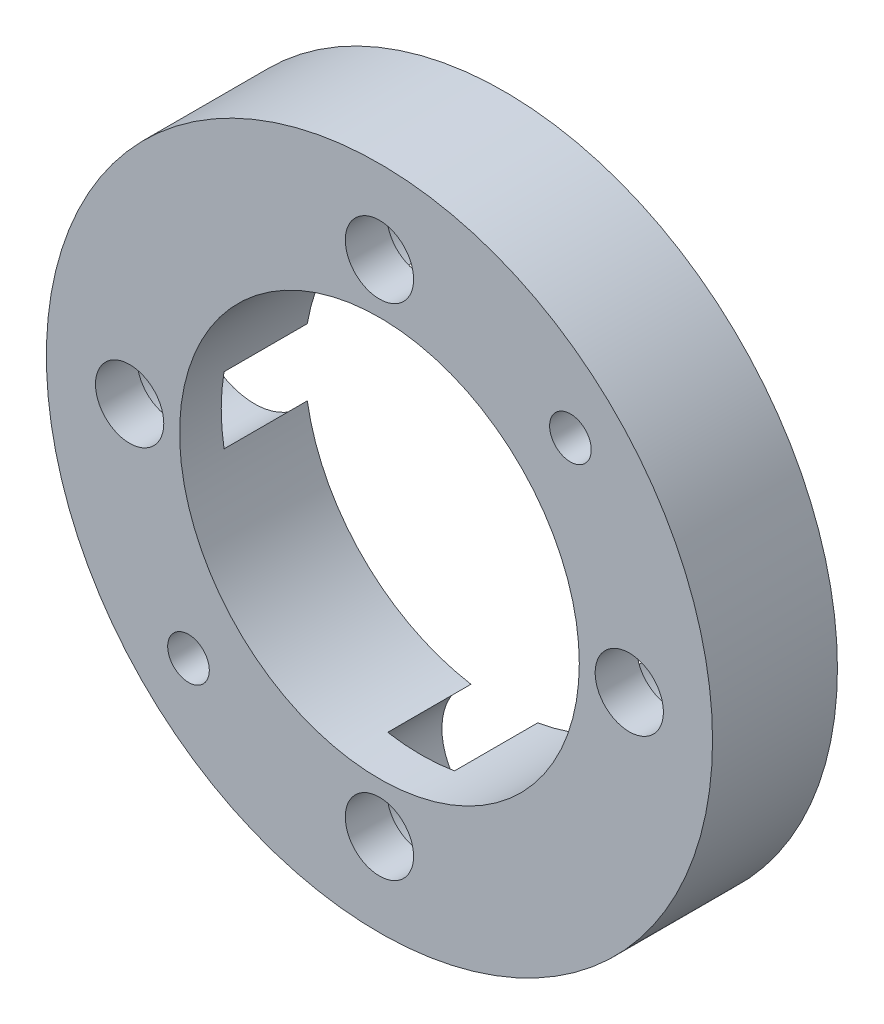
SolidWorks part; units mm, degrees
ref_plane "正面" through (0, 0, 0) normal (0, 0, 1) x (1, 0, 0)
ref_plane "平面" through (0, 0, 0) normal (0, 1, 0) x (1, 0, 0)
ref_plane "右側面" through (0, 0, 0) normal (1, 0, 0) x (0, 0, -1)
sketch "ｽｹｯﾁ1" plane through (0, 0, 0) normal (0, 0, 1) x (1, 0, 0)
  circle A0 centre (0, 0) radius 20
  circle A1 centre (0, 15) radius 2.05
  circle A2 centre (15, 0) radius 2.05
  circle A3 centre (0, -15) radius 2.05
  circle A4 centre (-15, 0) radius 2.05
  point P14 (0, 0)
  dimension "D1" = 40
  dimension "D2" = 15
  dimension "D3" = 4.1
  dimension "D4" = 4
extrude "ﾎﾞｽ - 押し出し1" add sketch "ｽｹｯﾁ1" along normal blind 7.5
sketch "ｽｹｯﾁ2" plane through (0, 0, 7.5) normal (0, 0, 1) x (1, 0, 0)
  line L0 (0, 9.6202) -> (0, 0) construction
  line L1 (0, 0) -> (11.4657, 11.4657) construction
  line L2 (0, 0) -> (-11.4657, -11.4657) construction
  circle A0 centre (11.4657, 11.4657) radius 1.25
  circle A1 centre (-11.4657, -11.4657) radius 1.25
  circle A2 centre (0, 0) radius 12
  dimension "D3" = 2.5
  dimension "D4" = 24
  dimension "D1" = 45
  dimension "D2" = 32.43
extrude "ｶｯﾄ - 押し出し1" cut sketch "ｽｹｯﾁ2" against normal through all
sketch "ｽｹｯﾁ4" plane through (0, 0, 0) normal (0, 0, -1) x (-1, 0, 0)
  circle A0 centre (0, 15) radius 3.75
  circle A1 centre (15, 0) radius 3.75
  circle A2 centre (0, -15) radius 3.75
  circle A3 centre (-15, 0) radius 3.75
  point P12 (0, 0)
  dimension "D1" = 7.5
  dimension "D2" = 4
extrude "ｶｯﾄ - 押し出し3" cut sketch "ｽｹｯﾁ4" against normal blind 5
